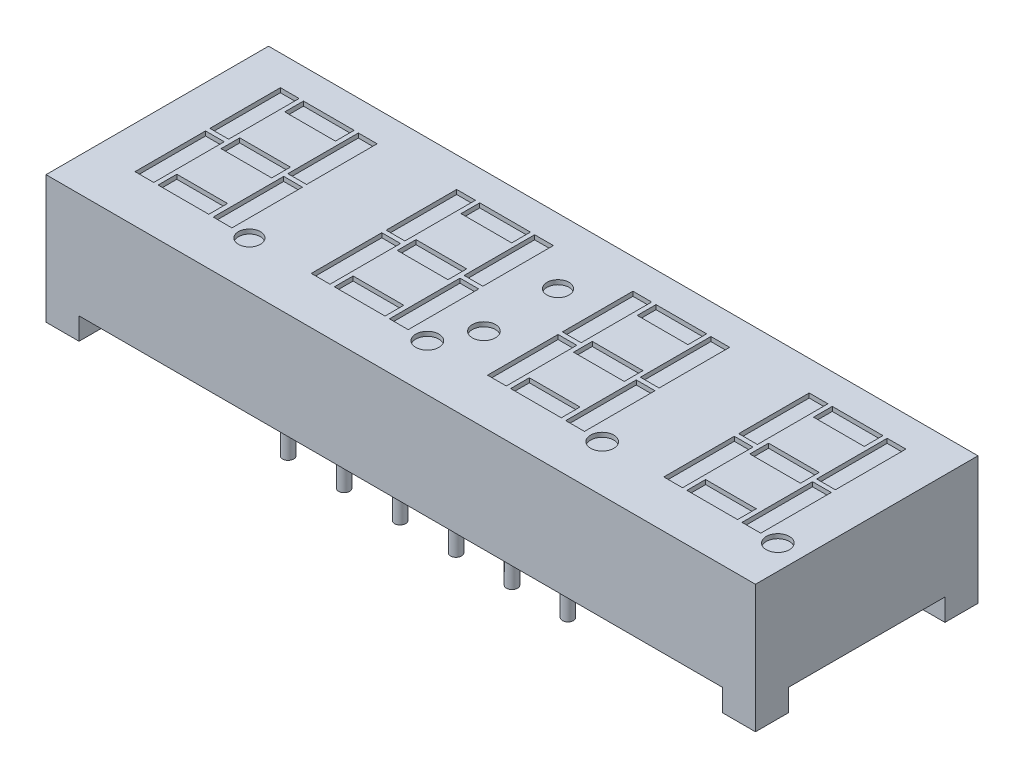
SolidWorks part; units mm, degrees
ref_plane "Спереди" through (0, 0, 0) normal (0, 0, 1) x (1, 0, 0)
ref_plane "Сверху" through (0, 0, 0) normal (0, 1, 0) x (1, 0, 0)
ref_plane "Справа" through (0, 0, 0) normal (1, 0, 0) x (0, 0, -1)
sketch "Эскиз1" plane through (0, 0, 0) normal (0, 1, 0) x (1, 0, 0)
  line L1 (-16.1, 5.05) -> (16.1, 5.05)
  line L2 (-16.1, 5.05) -> (-16.1, -5.05)
  line L3 (-16.1, -5.05) -> (16.1, -5.05)
  line L4 (16.1, 5.05) -> (16.1, -5.05)
  line L5 (-16.1, 5.05) -> (16.1, -5.05) construction
  line L6 (-16.1, -5.05) -> (16.1, 5.05) construction
  point P0 (0, 0)
  dimension "D1" = 10.1
  dimension "D2" = 32.2
extrude "Бобышка-Вытянуть1" add sketch "Эскиз1" along normal blind 5.8
sketch "Эскиз2" plane through (0, 0, 0) normal (0, -1, 0) x (1, 0, 0)
  line L0 (-16.1, 3.55) -> (-14.6, 3.55)
  line L1 (-16.1, -5.05) -> (-16.1, 5.05) construction
  line L2 (-14.6, 3.55) -> (-14.6, 5.05)
  line L3 (-16.1, 5.05) -> (16.1, 5.05) construction
  line L4 (-14.6, 5.05) -> (14.6, 5.05)
  line L5 (14.6, 5.05) -> (14.6, 3.55)
  line L6 (14.6, 3.55) -> (16.1, 3.55)
  line L7 (16.1, 5.05) -> (16.1, -5.05) construction
  line L8 (16.1, 3.55) -> (16.1, -3.55)
  line L9 (16.1, -3.55) -> (14.6, -3.55)
  line L10 (14.6, -3.55) -> (14.6, -5.05)
  line L11 (16.1, -5.05) -> (-16.1, -5.05) construction
  line L12 (14.6, -5.05) -> (-14.6, -5.05)
  line L13 (-14.6, -5.05) -> (-14.6, -3.55)
  line L14 (-14.6, -3.55) -> (-16.1, -3.55)
  line L15 (-16.1, -3.55) -> (-16.1, 3.55)
  dimension "D1" = 1.5
  dimension "D2" = 1.5
  dimension "D3" = 1.5
  dimension "D4" = 1.5
  dimension "D5" = 1.5
  dimension "D6" = 1.5
  dimension "D7" = 1.5
  dimension "D8" = 1.5
extrude "Вырез-Вытянуть1" cut sketch "Эскиз2" against normal blind 1
sketch "Эскиз3" plane through (0, 1, 0) normal (0, -1, 0) x (1, 0, 0)
  circle A0 centre (-6.35, 3.81) radius 0.25
  circle A1 centre (-3.81, 3.81) radius 0.25
  circle A2 centre (-1.27, 3.81) radius 0.25
  circle A3 centre (1.27, 3.81) radius 0.25
  circle A4 centre (3.81, 3.81) radius 0.25
  circle A5 centre (6.35, 3.81) radius 0.25
  circle A6 centre (-3.81, -3.81) radius 0.25
  circle A7 centre (-1.27, -3.81) radius 0.25
  circle A8 centre (1.27, -3.81) radius 0.25
  circle A9 centre (3.81, -3.81) radius 0.25
  circle A10 centre (6.35, -3.81) radius 0.25
  circle A11 centre (-6.35, -3.81) radius 0.25
  dimension "D1" = 0.5
  dimension "D4" = 3.81
  dimension "D5" = 6.35
  dimension "D2" = 6
  dimension "D3" = 2
extrude "Бобышка-Вытянуть2" add sketch "Эскиз3" along normal blind 2
sketch "Эскиз4" plane through (0, 5.8, 0) normal (0, 1, 0) x (1, 0, 0)
  line L0 (-14.1985, 0.2885) -> (-13.3485, 0.2885)
  line L1 (-13.15, 3.6857) -> (-10.85, 3.6857)
  line L2 (-13.15, 3.6857) -> (-13.15, 2.8357)
  line L3 (-13.15, 2.8357) -> (-10.85, 2.8357)
  line L4 (-10.85, 3.6857) -> (-10.85, 2.8357)
  line L5 (-13.15, 3.6857) -> (-10.85, 2.8357) construction
  line L6 (-13.15, 2.8357) -> (-10.85, 3.6857) construction
  line L7 (-14.2, 3.6885) -> (-13.35, 3.6885)
  line L8 (-14.2, 3.6885) -> (-14.2, 0.4885)
  line L9 (-14.2, 0.4885) -> (-13.35, 0.4885)
  line L10 (-13.35, 3.6885) -> (-13.35, 0.4885)
  line L11 (-14.2, 3.6885) -> (-13.35, 0.4885) construction
  line L12 (-14.2, 0.4885) -> (-13.35, 3.6885) construction
  line L17 (-14.1985, 0.2885) -> (-14.1985, -2.9115)
  line L18 (-14.1985, -2.9115) -> (-13.3485, -2.9115)
  line L19 (-13.3485, 0.2885) -> (-13.3485, -2.9115)
  line L20 (-10.65, 3.6774) -> (-9.8, 3.6774)
  line L21 (-10.65, 3.6774) -> (-10.65, 0.4774)
  line L22 (-10.65, 0.4774) -> (-9.8, 0.4774)
  line L23 (-9.8, 3.6774) -> (-9.8, 0.4774)
  line L24 (-10.6381, 0.2774) -> (-9.7881, 0.2774)
  line L25 (-10.6381, 0.2774) -> (-10.6381, -2.9226)
  line L26 (-10.6381, -2.9226) -> (-9.7881, -2.9226)
  line L27 (-9.7881, 0.2774) -> (-9.7881, -2.9226)
  line L28 (-13.15, 0.7935) -> (-10.85, 0.7935)
  line L29 (-13.15, 0.7935) -> (-13.15, -0.0565)
  line L30 (-13.15, -0.0565) -> (-10.85, -0.0565)
  line L31 (-10.85, 0.7935) -> (-10.85, -0.0565)
  line L32 (-13.1485, -2.0635) -> (-10.8485, -2.0635)
  line L33 (-13.1485, -2.0635) -> (-13.1485, -2.9135)
  line L34 (-13.1485, -2.9135) -> (-10.8485, -2.9135)
  line L35 (-10.8485, -2.0635) -> (-10.8485, -2.9135)
  line L36 (-6.1985, 0.2885) -> (-5.3485, 0.2885)
  line L37 (-5.15, 3.6857) -> (-2.85, 3.6857)
  line L38 (-5.15, 3.6857) -> (-5.15, 2.8357)
  line L39 (-5.15, 2.8357) -> (-2.85, 2.8357)
  line L40 (-2.85, 3.6857) -> (-2.85, 2.8357)
  line L41 (-6.2, 3.6885) -> (-5.35, 3.6885)
  line L42 (-6.2, 3.6885) -> (-6.2, 0.4885)
  line L43 (-6.2, 0.4885) -> (-5.35, 0.4885)
  line L44 (-5.35, 3.6885) -> (-5.35, 0.4885)
  line L45 (-6.1985, 0.2885) -> (-6.1985, -2.9115)
  line L46 (-6.1985, -2.9115) -> (-5.3485, -2.9115)
  line L47 (-5.3485, 0.2885) -> (-5.3485, -2.9115)
  line L48 (-2.65, 3.6774) -> (-1.8, 3.6774)
  line L49 (-2.65, 3.6774) -> (-2.65, 0.4774)
  line L50 (-2.65, 0.4774) -> (-1.8, 0.4774)
  line L51 (-1.8, 3.6774) -> (-1.8, 0.4774)
  line L52 (-2.6381, 0.2774) -> (-1.7881, 0.2774)
  line L53 (-2.6381, 0.2774) -> (-2.6381, -2.9226)
  line L54 (-2.6381, -2.9226) -> (-1.7881, -2.9226)
  line L55 (-1.7881, 0.2774) -> (-1.7881, -2.9226)
  line L56 (-5.15, 0.7935) -> (-2.85, 0.7935)
  line L57 (-5.15, 0.7935) -> (-5.15, -0.0565)
  line L58 (-5.15, -0.0565) -> (-2.85, -0.0565)
  line L59 (-2.85, 0.7935) -> (-2.85, -0.0565)
  line L60 (-5.1485, -2.0635) -> (-2.8485, -2.0635)
  line L61 (-5.1485, -2.0635) -> (-5.1485, -2.9135)
  line L62 (-5.1485, -2.9135) -> (-2.8485, -2.9135)
  line L63 (-2.8485, -2.0635) -> (-2.8485, -2.9135)
  line L64 (-5.15, 3.6857) -> (-2.85, 2.8357) construction
  line L65 (-5.15, 2.8357) -> (-2.85, 3.6857) construction
  line L66 (-6.2, 3.6885) -> (-5.35, 0.4885) construction
  line L67 (-6.2, 0.4885) -> (-5.35, 3.6885) construction
  line L68 (1.8015, 0.2885) -> (2.6515, 0.2885)
  line L69 (2.85, 3.6857) -> (5.15, 3.6857)
  line L70 (2.85, 3.6857) -> (2.85, 2.8357)
  line L71 (2.85, 2.8357) -> (5.15, 2.8357)
  line L72 (5.15, 3.6857) -> (5.15, 2.8357)
  line L73 (1.8, 3.6885) -> (2.65, 3.6885)
  line L74 (1.8, 3.6885) -> (1.8, 0.4885)
  line L75 (1.8, 0.4885) -> (2.65, 0.4885)
  line L76 (2.65, 3.6885) -> (2.65, 0.4885)
  line L77 (1.8015, 0.2885) -> (1.8015, -2.9115)
  line L78 (1.8015, -2.9115) -> (2.6515, -2.9115)
  line L79 (2.6515, 0.2885) -> (2.6515, -2.9115)
  line L80 (5.35, 3.6774) -> (6.2, 3.6774)
  line L81 (5.35, 3.6774) -> (5.35, 0.4774)
  line L82 (5.35, 0.4774) -> (6.2, 0.4774)
  line L83 (6.2, 3.6774) -> (6.2, 0.4774)
  line L84 (5.3619, 0.2774) -> (6.2119, 0.2774)
  line L85 (5.3619, 0.2774) -> (5.3619, -2.9226)
  line L86 (5.3619, -2.9226) -> (6.2119, -2.9226)
  line L87 (6.2119, 0.2774) -> (6.2119, -2.9226)
  line L88 (2.85, 0.7935) -> (5.15, 0.7935)
  line L89 (2.85, 0.7935) -> (2.85, -0.0565)
  line L90 (2.85, -0.0565) -> (5.15, -0.0565)
  line L91 (5.15, 0.7935) -> (5.15, -0.0565)
  line L92 (2.8515, -2.0635) -> (5.1515, -2.0635)
  line L93 (2.8515, -2.0635) -> (2.8515, -2.9135)
  line L94 (2.8515, -2.9135) -> (5.1515, -2.9135)
  line L95 (5.1515, -2.0635) -> (5.1515, -2.9135)
  line L96 (2.85, 3.6857) -> (5.15, 2.8357) construction
  line L97 (2.85, 2.8357) -> (5.15, 3.6857) construction
  line L98 (1.8, 3.6885) -> (2.65, 0.4885) construction
  line L99 (1.8, 0.4885) -> (2.65, 3.6885) construction
  line L100 (9.8015, 0.2885) -> (10.6515, 0.2885)
  line L101 (10.85, 3.6857) -> (13.15, 3.6857)
  line L102 (10.85, 3.6857) -> (10.85, 2.8357)
  line L103 (10.85, 2.8357) -> (13.15, 2.8357)
  line L104 (13.15, 3.6857) -> (13.15, 2.8357)
  line L105 (9.8, 3.6885) -> (10.65, 3.6885)
  line L106 (9.8, 3.6885) -> (9.8, 0.4885)
  line L107 (9.8, 0.4885) -> (10.65, 0.4885)
  line L108 (10.65, 3.6885) -> (10.65, 0.4885)
  line L109 (9.8015, 0.2885) -> (9.8015, -2.9115)
  line L110 (9.8015, -2.9115) -> (10.6515, -2.9115)
  line L111 (10.6515, 0.2885) -> (10.6515, -2.9115)
  line L112 (13.35, 3.6774) -> (14.2, 3.6774)
  line L113 (13.35, 3.6774) -> (13.35, 0.4774)
  line L114 (13.35, 0.4774) -> (14.2, 0.4774)
  line L115 (14.2, 3.6774) -> (14.2, 0.4774)
  line L116 (13.3619, 0.2774) -> (14.2119, 0.2774)
  line L117 (13.3619, 0.2774) -> (13.3619, -2.9226)
  line L118 (13.3619, -2.9226) -> (14.2119, -2.9226)
  line L119 (14.2119, 0.2774) -> (14.2119, -2.9226)
  line L120 (10.85, 0.7935) -> (13.15, 0.7935)
  line L121 (10.85, 0.7935) -> (10.85, -0.0565)
  line L122 (10.85, -0.0565) -> (13.15, -0.0565)
  line L123 (13.15, 0.7935) -> (13.15, -0.0565)
  line L124 (10.8515, -2.0635) -> (13.1515, -2.0635)
  line L125 (10.8515, -2.0635) -> (10.8515, -2.9135)
  line L126 (10.8515, -2.9135) -> (13.1515, -2.9135)
  line L127 (13.1515, -2.0635) -> (13.1515, -2.9135)
  line L128 (10.85, 3.6857) -> (13.15, 2.8357) construction
  line L129 (10.85, 2.8357) -> (13.15, 3.6857) construction
  line L130 (9.8, 3.6885) -> (10.65, 0.4885) construction
  line L131 (9.8, 0.4885) -> (10.65, 3.6885) construction
  circle A0 centre (0, 2.0885) radius 0.5
  circle A1 centre (-8.9942, -2.9226) radius 0.5
  circle A2 centre (-0.0097, -1.2639) radius 0.5245
  circle A3 centre (-0.9191, -2.9226) radius 0.5245
  circle A4 centre (14.9884, -2.9226) radius 0.5245
  circle A5 centre (7.0177, -2.9226) radius 0.5245
  point P4 (-12, 3.2607)
  point P5 (-13.775, 2.0885)
  point P35 (0, -1.2516)
  point P36 (0, 2.0885)
  point P37 (-4, 3.2607)
  point P38 (-5.775, 2.0885)
  point P67 (4, 3.2607)
  point P68 (2.225, 2.0885)
  point P97 (12, 3.2607)
  point P98 (10.225, 2.0885)
  point P127 (0, 0)
  point P132 (-0.9191, -2.9226)
  point P133 (-8.9942, -2.9226)
  point P138 (7.0177, -2.9226)
  point P139 (14.9884, -2.9226)
  dimension "D13" = 1
  dimension "D14" = 1
  dimension "D1" = 3.2
  dimension "D2" = 0.85
  dimension "D3" = 2.3
  dimension "D4" = 0.85
  dimension "D5" = 0.2
  dimension "D6" = 0.2
  dimension "D7" = 0.2
  dimension "D8" = 0.2
  dimension "D9" = 12
  dimension "D10" = 0.2
  dimension "D11" = 0.2
  dimension "D12" = 4
extrude "Вырез-Вытянуть2" cut sketch "Эскиз4" against normal blind 0.2
